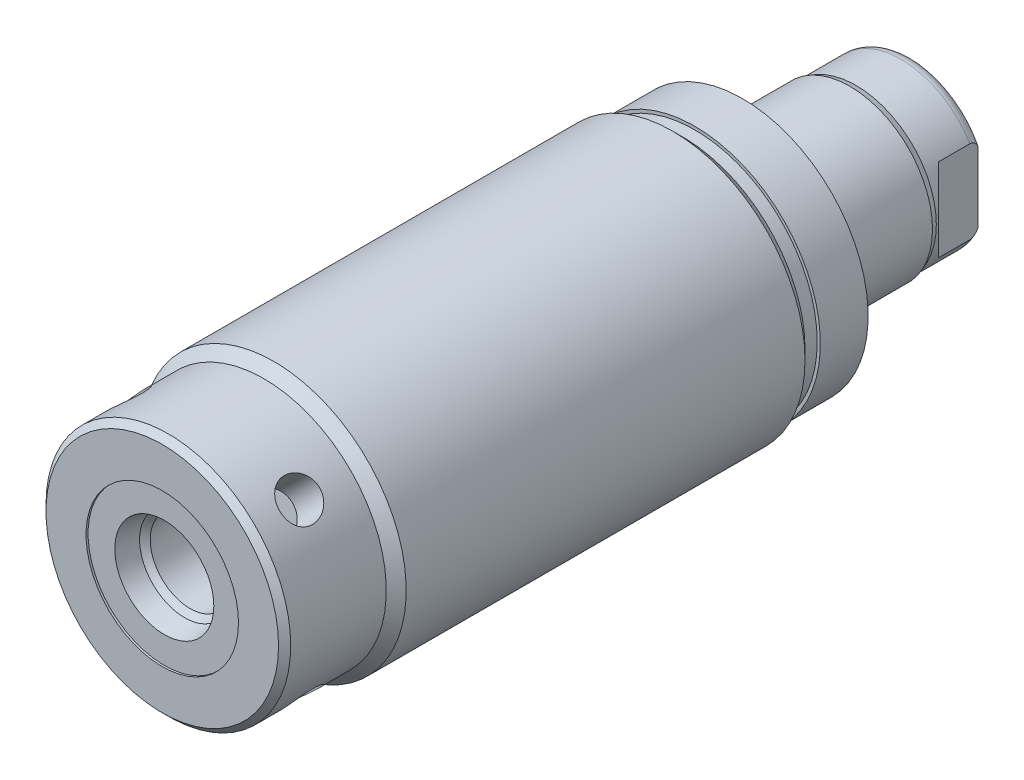
SolidWorks part; units mm, degrees
material "Alloy Steel"
ref_plane "Front Plane" through (0, 0, 0) normal (0, 0, 1) x (1, 0, 0)
ref_plane "Top Plane" through (0, 0, 0) normal (0, 1, 0) x (1, 0, 0)
ref_plane "Right Plane" through (0, 0, 0) normal (1, 0, 0) x (0, 0, -1)
ref_plane "Plane1" through (0, 0, 0) normal (0, 0, 1) x (1, 0, 0)
sketch "Sketch1" plane through (0, 0, 0) normal (0, 0, 1) x (1, 0, 0)
  circle A0 centre (0, 0) radius 16.5354
  dimension "D1" = 33.0708
extrude "Extrude1" add sketch "Sketch1" along normal blind 66.548
sketch "Sketch2" plane through (0, 0, 0) normal (0, 1, 0) x (1, 0, 0)
  line L0 (16.5354, -66.548) -> (16.5354, -52.6034)
  line L1 (16.5354, -52.6034) -> (15.2908, -53.848)
  line L2 (15.2908, -53.848) -> (15.2908, -66.548)
  line L3 (15.2908, -66.548) -> (16.5354, -66.548)
  line L4 (0, 0) -> (0, -24.4965) construction
  line L5 (-16.5354, -66.548) -> (16.5354, -66.548) construction
  line L6 (16.5354, -66.548) -> (16.5354, 0) construction
  dimension "D1" = 12.7
  dimension "D2" = 30.5816
  dimension "D3" = 45
revolve "Cut-Revolve1" cut sketch "Sketch2" angle 360 about L4
sketch "Sketch3" plane through (0, 0, 0) normal (0, 1, 0) x (1, 0, 0)
  line L0 (15.2908, 0) -> (15.2908, -1.524)
  line L1 (15.2908, -1.524) -> (16.5354, -2.7686)
  line L2 (16.5354, -2.7686) -> (16.5354, 0)
  line L3 (16.5354, 0) -> (15.2908, 0)
  line L4 (0, 0) -> (0, 3.0455) construction
  line L5 (15.2908, -66.548) -> (15.2908, -53.848) construction
  line L6 (16.5354, 0) -> (-16.5354, 0) construction
  line L7 (16.5354, -52.6034) -> (16.5354, 0) construction
  dimension "D1" = 45
  dimension "D2" = 1.524
revolve "Cut-Revolve2" cut sketch "Sketch3" angle 360 about L4
sketch "S2D0002" plane through (0, 0, 0) normal (0, 1, 0) x (1, 0, 0)
  line L0 (6.1849, -66.294) -> (9.525, -66.294)
  line L1 (6.1849, -66.294) -> (5.6423, -63.7413)
  line L2 (5.6423, -63.7413) -> (4.9784, -63.0774)
  line L3 (4.9784, -63.0774) -> (4.9784, -52.324)
  line L4 (4.9784, -52.324) -> (0, -52.324)
  line L5 (0, -52.324) -> (0, -66.548)
  line L6 (0, -14.6685) -> (0, 0.6985) construction
  line L8 (9.525, -66.294) -> (9.525, -66.548)
  line L9 (-15.2908, -66.548) -> (15.2908, -66.548) construction
  line L10 (9.525, -66.548) -> (0, -66.548)
  dimension "D1" = 19.05
  dimension "D2" = 9.9568
  dimension "D3" = 0.254
  dimension "D4" = 12.3698
  dimension "D5" = 12
  dimension "D6" = 45
  dimension "D7" = 2.5527
  dimension "D8" = 13.97
revolve "Cut-Revolve3" cut sketch "S2D0002" angle 360 about L6
chamfer "Chamfer1" distance 0.762 angle 45 1 edges at (-15.2908, 0, 66.548)
sketch "Sketch6" plane through (0, 0, 0) normal (0, 0, -1) x (-1, 0, 0)
  circle A0 centre (0, 0) radius 15.6845
  circle A1 centre (0, 0) radius 16.5354 construction
  dimension "D1" = 31.369
extrude "Extrude2" add sketch "Sketch6" along normal blind 5.969
sketch "Sketch7" plane through (0, 0, 0) normal (1, 0, 0) x (0, 0, -1)
  line L0 (5.969, 0) -> (5.969, -10.3187)
  line L1 (5.969, -10.3187) -> (26.797, -10.3187)
  line L2 (26.797, -10.3187) -> (26.797, 0)
  line L3 (26.797, 0) -> (5.969, 0)
  line L4 (0, 0) -> (9.7123, 0) construction
  line L5 (5.969, -15.6845) -> (5.969, 15.6845) construction
  dimension "D1" = 20.6375
  dimension "D2" = 20.828
revolve "Revolve1" add sketch "Sketch7" angle 360 about L4
sketch "S2D0001" plane through (0, 0, 0) normal (0, 1, 0) x (1, 0, 0)
  line L0 (3.2639, 24.8613) -> (3.2639, 11.9888)
  line L1 (3.2639, 11.9888) -> (0, 11.9888)
  line L2 (4.3815, 26.797) -> (0, 26.797)
  line L3 (0, 26.797) -> (0, 11.9888)
  line L4 (3.2639, 24.8613) -> (4.3815, 26.797)
  line L5 (0, -31.3084) -> (0, 2.765) construction
  line L6 (10.3188, 26.797) -> (-10.3188, 26.797) construction
  dimension "D1" = 8.763
  dimension "D2" = 30
  dimension "D3" = 14.8082
  dimension "D4" = 6.5278
revolve "Cut-Revolve5" cut sketch "S2D0001" angle 360 about L5
ref_plane "Plane8" through (0, 0, 0) normal (1, 0, 0) x (0, -1, 0)
sketch "Sketch9" plane through (0, 0, 0) normal (1, 0, 0) x (0, -1, 0)
  line L0 (-10.3188, 19.3802) -> (-10.033, 20.1422)
  line L1 (-10.033, 20.1422) -> (-10.033, 25.781)
  line L2 (0, 12.6594) -> (0, 20.8178) construction
  line L3 (10.3187, 26.797) -> (-10.3188, 26.797) construction
  line L4 (-9.6449, 26.797) -> (-10.3188, 26.797)
  line L5 (-10.3188, 26.797) -> (-10.3188, 19.3802)
  arc A0 (-9.6449, 26.797) -> (-10.033, 25.781) centre (-8.509, 25.781) ccw
  dimension "D1" = 1.524
  dimension "D2" = 1.016
  dimension "D3" = 20.066
  dimension "D4" = 0.762
  dimension "D5" = 7.4168
revolve "Cut-Revolve6" cut sketch "Sketch9" angle 360 about L2
sketch "Sketch13" plane through (0, 0, 0) normal (0, 1, 0) x (1, 0, 0)
  line L0 (8.5852, 26.797) -> (8.5852, 21.844)
  line L1 (8.5852, 21.844) -> (10.033, 20.3962)
  line L2 (-8.5852, 26.797) -> (-8.5852, 21.844)
  line L3 (-8.5852, 21.844) -> (-10.033, 20.3962)
  line L4 (9.6449, 26.797) -> (-9.6449, 26.797) construction
  line L5 (0, 13.7262) -> (0, 20.767) construction
  line L6 (10.033, 20.3962) -> (10.033, 26.797)
  line L8 (8.5852, 26.797) -> (10.033, 26.797)
  line L9 (10.033, 20.1422) -> (10.033, 25.781) construction
  line L10 (-10.033, 20.3962) -> (-10.033, 26.797)
  line L11 (-8.5852, 26.797) -> (-10.033, 26.797)
  dimension "D1" = 17.1704
  dimension "D2" = 135
  dimension "D3" = 4.953
extrude "Cut-Extrude4" cut sketch "Sketch13" against normal mid plane 39.685
ref_plane "Plane13" through (0, 0, 0) normal (0.7071, 0.7071, 0) x (0, 0, -1)
hole_wizard "Hole1" positions "3DSketch2" profile "Sketch14" legacy
sketch3d "3DSketch2"
  point P0 (-10.8122, 10.8122, 60.198)
  dimension "D1" = 6.35
sketch "Sketch14" plane through (-10.8122, 10.8122, 60.198) normal (0, 0, 1) x (-0.7071, -0.7071, 0)
  line L0 (0, 0) -> (0, 4.7498)
  line L1 (0, 4.7498) -> (2.5019, 4.7498)
  line L2 (2.5019, 4.7498) -> (2.5019, 0)
  line L3 (2.5019, 0) -> (0, 0)
  line L4 (0, 110) -> (0, -10) construction
  dimension "Diameter" = 5.0038
  dimension "Depth" = 4.7498
pattern_circular "CirPattern1" count 4 over 360 about axis through (0, 0, 0) along (0, 0, 1) of "Hole1"
